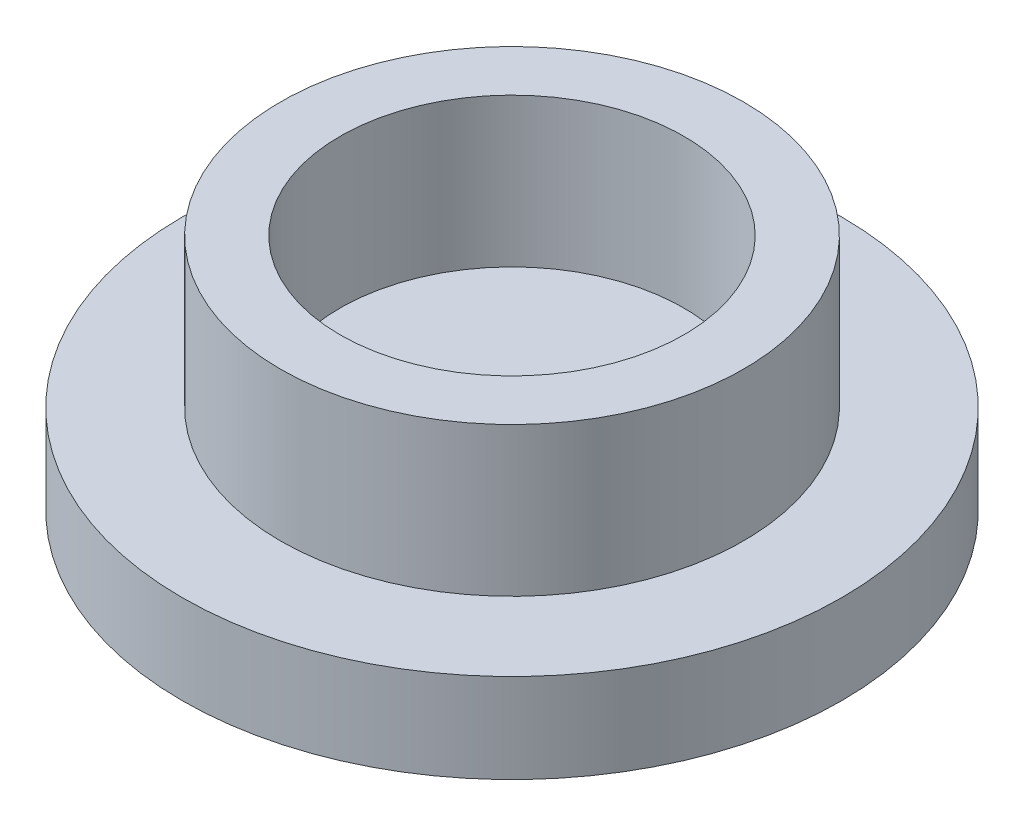
SolidWorks part; units mm, degrees
ref_plane "Front Plane" through (0, 0, 0) normal (0, 0, 1) x (1, 0, 0)
ref_plane "Top Plane" through (0, 0, 0) normal (0, 1, 0) x (1, 0, 0)
ref_plane "Right Plane" through (0, 0, 0) normal (1, 0, 0) x (0, 0, -1)
sketch "Sketch1" plane through (0, 0, 0) normal (0, 1, 0) x (1, 0, 0)
  circle A0 centre (0, 0) radius 8.08 construction
  circle A1 centre (0, 0) radius 11.08
  dimension "D1" = 16.16
  dimension "D2" = 3
extrude "Boss-Extrude1" add sketch "Sketch1" along normal blind 3
sketch "Sketch2" plane through (0, 3, 0) normal (0, 1, 0) x (1, 0, 0)
  circle A1 centre (0, 0) radius 7.78
  circle A2 centre (0, 0) radius 8.08
  circle A3 centre (0, 0) radius 8.08 construction
  circle A4 centre (0, 0) radius 5.78
  dimension "D1" = 3
  dimension "D2" = 0.3
  dimension "D3" = 2
extrude "Boss-Extrude2" add sketch "Sketch2" along normal blind 5
